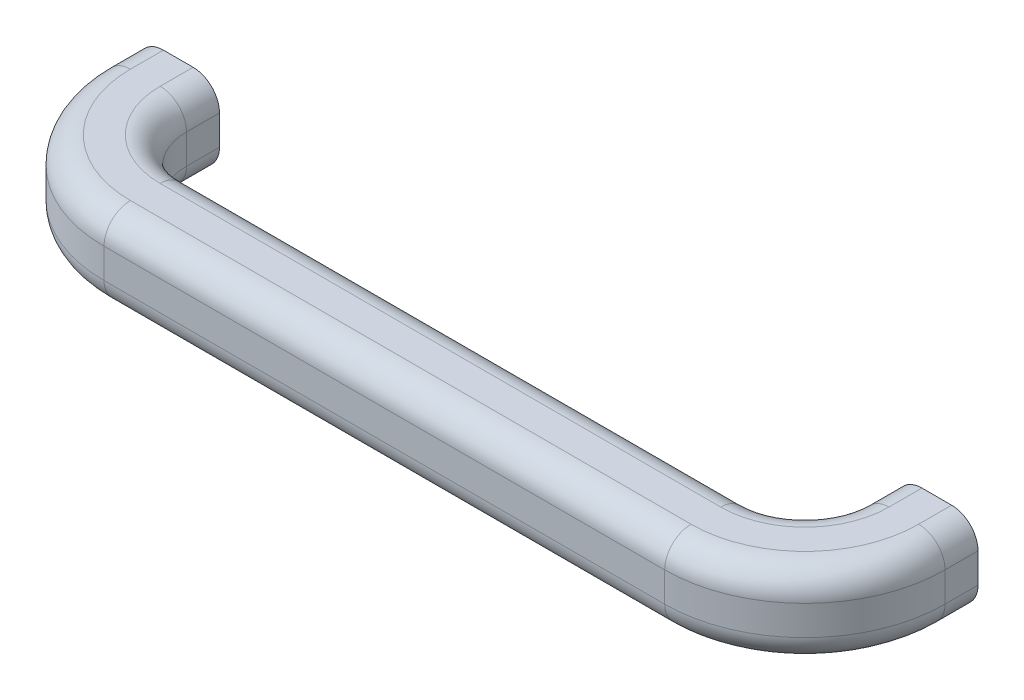
SolidWorks part; units mm, degrees
ref_plane "Front Plane" through (0, 0, 0) normal (0, 0, 1) x (1, 0, 0)
ref_plane "Top Plane" through (0, 0, 0) normal (0, 1, 0) x (1, 0, 0)
ref_plane "Right Plane" through (0, 0, 0) normal (1, 0, 0) x (0, 0, -1)
sketch "Sketch2" plane through (0, 0, 0) normal (0, 1, 0) x (1, 0, 0)
  line L2 (0, 30) -> (0, 157.2895)
  line L3 (0, 157.2895) -> (0, 169.7895)
  line L4 (0, 169.7895) -> (8.8388, 160.9507) construction
  line L5 (8.8388, 160.9507) -> (-8.8388, 178.6284) construction
  line L8 (-200, 0) -> (-30, 0)
  line L9 (-230, 40) -> (-230, 30)
  line L10 (0, 0) -> (-486.1041, 0) construction
  line L11 (-486.1041, 0) -> (-486.1041, 40) construction
  line L12 (-486.1041, 40) -> (-230, 40) construction
  arc A0 (0, 30) -> (-30, 0) centre (-30, 30) cw
  arc A1 (-200, 0) -> (-230, 30) centre (-200, 30) cw
  point P4 (0, 169.7895)
  point P15 (36.0638, 0)
  dimension "D8" = 30
  dimension "D3" = 30
  dimension "D1" = 40
  dimension "D4" = 12.5
  dimension "D5" = 25
  dimension "D7" = 200
ref_plane "Plane1" through (0, 0, -40) normal (0, 0, 1) x (1, 0, 0)
sketch "Sketch6" plane through (0, 0, -40) normal (0, 0, 1) x (1, 0, 0)
  line L1 (-234.5, -9.5) -> (-225.5, -9.5)
  line L2 (-239.5, -4.5) -> (-239.5, 4.5)
  line L3 (-234.5, 9.5) -> (-225.5, 9.5)
  line L4 (-220.5, -4.5) -> (-220.5, 4.5)
  line L5 (-239.5, -9.5) -> (-220.5, 9.5) construction
  line L6 (-239.5, 9.5) -> (-220.5, -9.5) construction
  arc A0 (-220.5, -4.5) -> (-225.5, -9.5) centre (-225.5, -4.5) cw
  arc A1 (-234.5, -9.5) -> (-239.5, -4.5) centre (-234.5, -4.5) cw
  arc A2 (-239.5, 4.5) -> (-234.5, 9.5) centre (-234.5, 4.5) cw
  arc A3 (-225.5, 9.5) -> (-220.5, 4.5) centre (-225.5, 4.5) cw
  point P0 (-230, 0)
  dimension "D3" = 5
  dimension "D1" = 19
  dimension "D2" = 19
sweep "Sweep-Thin1" add profiles "Sketch6" path "Sketch2" parameters "D1"=3
sketch "Sketch11" plane through (0, 0, -40) normal (0, 0, 1) x (1, 0, 0)
  line L1 (-30.8038, 301.3397) -> (454.9899, 301.3397)
  line L2 (-30.8038, 301.3397) -> (-30.8038, -294.6206)
  line L3 (-30.8038, -294.6206) -> (454.9899, -294.6206)
  line L4 (454.9899, 301.3397) -> (454.9899, -294.6206)
  line L5 (-30.8038, 301.3397) -> (454.9899, -294.6206) construction
  line L6 (-30.8038, -294.6206) -> (454.9899, 301.3397) construction
  point P0 (212.093, 3.3595)
extrude "Cut-Extrude1" cut sketch "Sketch11" against normal through all
ref_plane "Plane2" through (0, -22.5, 0) normal (0, -1, 0) x (-1, 0, 0)
sketch "Sketch12" plane through (0, -22.5, 0) normal (0, -1, 0) x (-1, 0, 0)
  line L0 (0, 0) -> (160, 0) construction
  line L1 (160, 0) -> (160, -55.5646) construction
  dimension "D1" = 160
